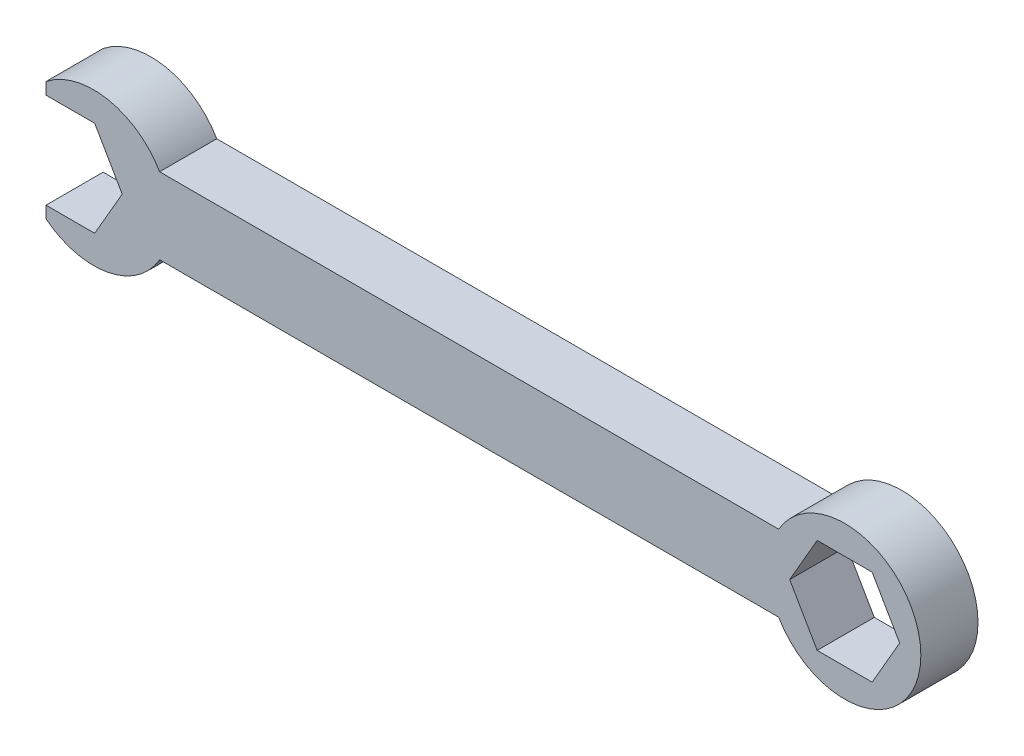
SolidWorks part; units mm, degrees
material "Cast Alloy Steel"
ref_plane "Front Plane" through (0, 0, 0) normal (0, 0, 1) x (1, 0, 0)
ref_plane "Top Plane" through (0, 0, 0) normal (0, 1, 0) x (1, 0, 0)
ref_plane "Right Plane" through (0, 0, 0) normal (1, 0, 0) x (0, 0, -1)
sketch "Sketch1" plane through (0, 0, 0) normal (0, 0, 1) x (1, 0, 0)
  line L0 (-8.7988, 5.08) -> (-91.3488, 5.08)
  line L1 (7.3323, 0) -> (3.6662, 6.35)
  line L2 (3.6662, 6.35) -> (-3.6662, 6.35)
  line L3 (-3.6662, 6.35) -> (-7.3323, 0)
  line L4 (-7.3323, 0) -> (-3.6662, -6.35)
  line L5 (-3.6662, -6.35) -> (3.6662, -6.35)
  line L6 (3.6662, -6.35) -> (7.3323, 0)
  line L7 (-91.3488, -5.08) -> (-8.7988, -5.08)
  line L8 (-106.4976, 9.5673) -> (-106.4976, -16.4357)
  line L15 (-96.3376, 0) -> (-100.0038, 6.35)
  line L16 (-100.0038, 6.35) -> (-107.3362, 6.35)
  line L17 (-107.3362, 6.35) -> (-111.0023, 0)
  line L18 (-111.0023, 0) -> (-107.3362, -6.35)
  line L19 (-107.3362, -6.35) -> (-100.0038, -6.35)
  line L20 (-100.0038, -6.35) -> (-96.3376, 0)
  arc A0 (-8.7988, -5.08) -> (-8.7988, 5.08) centre (0, 0) ccw
  circle A1 centre (0, 0) radius 6.35 construction
  arc A2 (-91.3488, 5.08) -> (-91.3488, -5.08) centre (-100.1476, 0) ccw
  circle A3 centre (-103.67, 0) radius 6.35 construction
  point P1 (0, 0)
  point P26 (0, 0)
  point P27 (0, 0)
  point P28 (0, 0)
  point P29 (0, 0)
  dimension "D2" = 20.32
  dimension "D5" = 20.32
  dimension "D1" = 82.55
  dimension "D3" = 12.7
  dimension "D4" = 10.16
  dimension "D6" = 12.7
  dimension "D7" = 6.35
  dimension "D8" = 10.16
  dimension "D9" = 5.08
extrude "Boss-Extrude1" add sketch "Sketch1" along normal blind 7.62 contours L0 A2 L8 L16 L15 L20 L19 L7 A0 L6 L5 L4 L3 L2 L1
